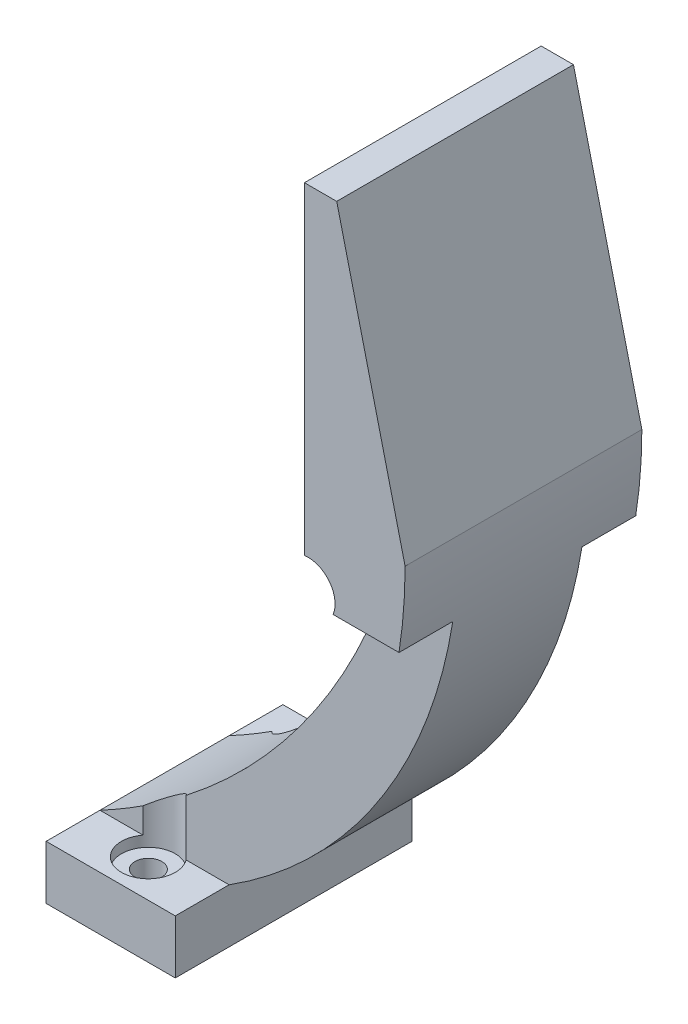
SolidWorks part; units mm, degrees
ref_plane "Plan de face" through (0, 0, 0) normal (0, 0, 1) x (1, 0, 0)
ref_plane "Plan de dessus" through (0, 0, 0) normal (0, 1, 0) x (1, 0, 0)
ref_plane "Plan de droite" through (0, 0, 0) normal (1, 0, 0) x (0, 0, -1)
sketch "Esquisse1" plane through (0, 0, 0) normal (0, 0, 1) x (1, 0, 0)
  line L1 (0, 0) -> (0, 5)
  line L2 (24, 40) -> (24, 70)
  line L3 (24, 70) -> (27, 70)
  line L4 (27, 70) -> (33.3552, 43.8163)
  line L5 (0, 0) -> (12, 0)
  line L6 (12, 0) -> (12, 5)
  arc A0 (0, 5) -> (26.6648, 36.5849) centre (-26.3061, 54.2562) ccw
  arc A1 (26.6648, 36.5849) -> (24, 40) centre (24.348, 37.5243) ccw
  arc A2 (12, 5) -> (33.3552, 43.8163) centre (-12.5436, 43.7855) ccw
  point P8 (0, 0)
  point P13 (21.1082, 70)
  point P14 (0, 0)
  point P15 (0, 0)
  point P16 (0, 0)
  dimension "D4" = 2.5
  dimension "D1" = 12
  dimension "D2" = 70
  dimension "D3" = 30
  dimension "D5" = 5
  dimension "D6" = 5
  dimension "D7" = 3
  dimension "24" = 24
extrude "Boss.-Extru.1" add sketch "Esquisse1" along normal blind 22
sketch "Esquisse2" plane through (0, 0, 0) normal (-1, 0, 0) x (0, 0, 1)
  line L0 (11, 5) -> (5, 5) construction
  line L1 (22, 5) -> (0, 5) construction
  line L2 (11, 5) -> (17, 5) construction
  line L3 (5, 5) -> (0, 5)
  line L4 (5, 5) -> (5, 36.5849)
  line L5 (5, 36.5849) -> (0, 36.5849)
  line L6 (0, 5) -> (0, 36.5849)
  line L8 (17, 5) -> (22, 5)
  line L9 (17, 5) -> (17, 36.5849)
  line L10 (17, 36.5849) -> (22, 36.5849)
  line L11 (22, 5) -> (22, 36.5849)
  dimension "D1" = 6
  dimension "D2" = 6
extrude "Enlèv. mat.-Extru.1" cut sketch "Esquisse2" against normal up to next
sketch "Esquisse3" plane through (0, 0, 0) normal (0, -1, 0) x (1, 0, 0)
  line L0 (6, 22) -> (6, 18.5) construction
  line L1 (0, 22) -> (12, 22) construction
  line L2 (6, 0) -> (6, 3.5) construction
  line L3 (0, 0) -> (12, 0) construction
  circle A0 centre (6, 18.5) radius 1.25
  circle A1 centre (6, 3.5) radius 1.25
  dimension "D3" = 2.5
  dimension "D4" = 2.5
  dimension "D1" = 3.5
  dimension "D2" = 3.5
extrude "Enlèv. mat.-Extru.2" cut sketch "Esquisse3" against normal blind 4
sketch "Esquisse5" plane through (0, 4, 0) normal (0, -1, 0) x (-1, 0, 0)
  circle A0 centre (-6, -3.5) radius 2.5
  circle A1 centre (-6, -18.5) radius 2.5
  dimension "D1" = 5
  dimension "D2" = 5
extrude "Enlèv. mat.-Extru.3" cut sketch "Esquisse5" against normal up to next
